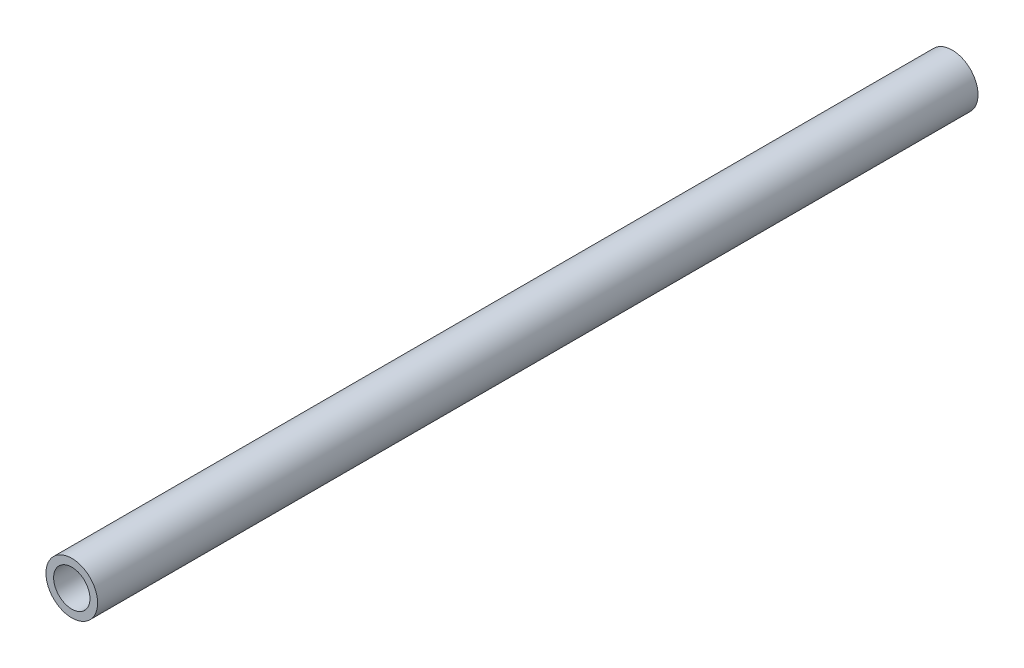
SolidWorks part; units mm, degrees
material "Galvanized Steel"
ref_plane "Front Plane" through (0, 0, 0) normal (0, 0, 1) x (1, 0, 0)
ref_plane "Top Plane" through (0, 0, 0) normal (0, 1, 0) x (1, 0, 0)
ref_plane "Right Plane" through (0, 0, 0) normal (1, 0, 0) x (0, 0, -1)
sketch "Sketch1" plane through (0, 0, 0) normal (0, 0, 1) x (1, 0, 0)
  circle A0 centre (347.5, -20) radius 13.5
  circle A1 centre (347.5, -20) radius 9.5
  circle A2 centre (347.5, -20) radius 14 construction
  dimension "D1" = 27
  dimension "D2" = 19
extrude "Boss-Extrude1" add sketch "Sketch1" along normal up to surface (460 mm away)
